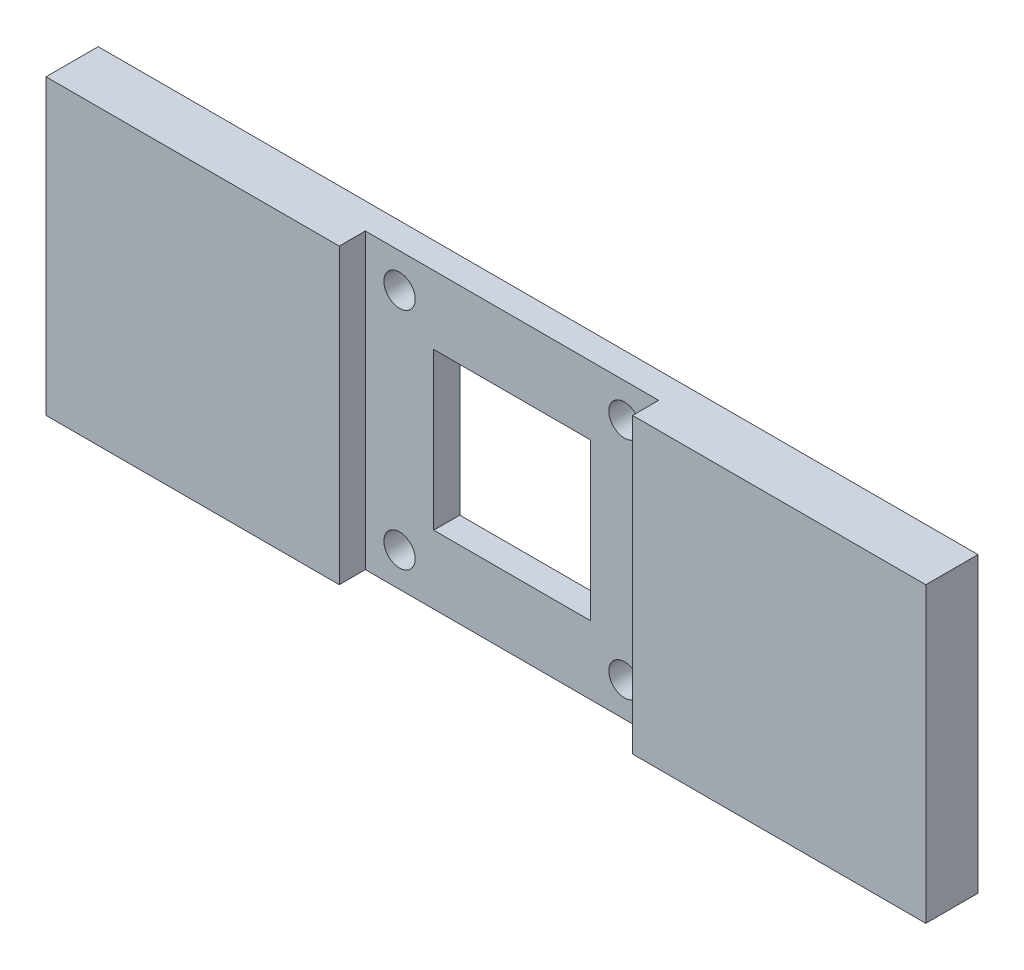
SolidWorks part; units mm, degrees
ref_plane "Front Plane" through (0, 0, 0) normal (0, 0, 1) x (1, 0, 0)
ref_plane "Top Plane" through (0, 0, 0) normal (0, 1, 0) x (1, 0, 0)
ref_plane "Right Plane" through (0, 0, 0) normal (1, 0, 0) x (0, 0, -1)
sketch "Sketch1" plane through (0, 0, 0) normal (0, 0, 1) x (1, 0, 0)
  line L1 (-175, -28.1) -> (175, -28.1)
  line L2 (-175, -28.1) -> (-175, 28.1)
  line L3 (-175, 28.1) -> (175, 28.1)
  line L4 (175, -28.1) -> (175, 28.1)
  line L5 (-175, -28.1) -> (175, 28.1) construction
  line L6 (-175, 28.1) -> (175, -28.1) construction
  point P0 (0, 0)
extrude "Boss-Extrude1" add sketch "Sketch1" along normal blind 10
sketch "Sketch2" plane through (0, 0, 10) normal (0, 0, 1) x (1, 0, 0)
  line L2 (175, 28.1) -> (-175, 28.1) construction
  line L3 (-28.1, -28.1) -> (28.1, -28.1)
  line L4 (-28.1, -28.1) -> (-28.1, 28.1)
  line L5 (-28.1, 28.1) -> (28.1, 28.1)
  line L6 (28.1, -28.1) -> (28.1, 28.1)
  point P8 (0, 0)
extrude "Cut-Extrude1" cut sketch "Sketch2" against normal blind 5
sketch "Sketch3" plane through (175, 0, 0) normal (1, 0, 0) x (0, 0, -1)
  line L1 (-10, 28.1) -> (0, 28.1)
  line L2 (-10, 28.1) -> (-10, -28.1)
  line L3 (-10, -28.1) -> (0, -28.1)
  line L4 (0, 28.1) -> (0, -28.1)
extrude "Boss-Extrude2" add sketch "Sketch3" along normal blind 10
sketch "Sketch4" plane through (0, 0, 10) normal (0, 0, 1) x (1, 0, 0)
  line L0 (28.1, -28.1) -> (185, -28.1) construction
  line L1 (185, 28.1) -> (175, 28.1)
  line L2 (185, 28.1) -> (185, -28.1)
  line L3 (185, -28.1) -> (175, -28.1)
  line L4 (175, 28.1) -> (175, -28.1)
extrude "Boss-Extrude3" add sketch "Sketch4" along normal blind 10
sketch "Sketch5" plane through (0, 28.1, 0) normal (0, 1, 0) x (1, 0, 0)
  line L0 (175, -20) -> (185, -10)
  line L1 (185, 0) -> (185, -20) construction
  line L2 (185, -10) -> (185, -20)
  line L3 (185, -20) -> (175, -20)
extrude "Cut-Extrude2" cut sketch "Sketch5" against normal blind 56.2
sketch "Sketch6" plane through (-175, 0, 0) normal (-1, 0, 0) x (0, 0, 1)
  line L1 (0, -28.1) -> (10, -28.1)
  line L2 (0, -28.1) -> (0, 28.1)
  line L3 (0, 28.1) -> (10, 28.1)
  line L4 (10, -28.1) -> (10, 28.1)
extrude "Boss-Extrude4" add sketch "Sketch6" along normal blind 10
sketch "Sketch7" plane through (0, 0, 10) normal (0, 0, 1) x (1, 0, 0)
  line L0 (-28.1, 28.1) -> (-185, 28.1) construction
  line L1 (-185, -28.1) -> (-175, -28.1)
  line L2 (-185, -28.1) -> (-185, 28.1)
  line L3 (-185, 28.1) -> (-175, 28.1)
  line L4 (-175, -28.1) -> (-175, 28.1)
extrude "Boss-Extrude5" add sketch "Sketch7" along normal blind 10
sketch "Sketch8" plane through (0, 28.1, 0) normal (0, 1, 0) x (1, 0, 0)
  line L0 (-175, -20) -> (-185, -10)
  line L1 (-185, -20) -> (-185, 0) construction
  line L2 (-185, -10) -> (-185, -20)
  line L3 (-185, -20) -> (-175, -20)
extrude "Cut-Extrude3" cut sketch "Sketch8" against normal blind 56.2
sketch "Sketch9" plane through (0, 0, 5) normal (0, 0, 1) x (1, 0, 0)
  line L3 (-15, -15) -> (15, -15)
  line L4 (-15, -15) -> (-15, 15)
  line L5 (-15, 15) -> (15, 15)
  line L6 (15, -15) -> (15, 15)
  point P4 (0, 0)
extrude "Cut-Extrude4" cut sketch "Sketch9" against normal blind 5
sketch "Sketch10" plane through (0, 0, 5) normal (0, 0, 1) x (1, 0, 0)
  circle A2 centre (21.55, 21.55) radius 3
  circle A3 centre (-21.55, -21.55) radius 3
  circle A4 centre (-21.55, 21.55) radius 3
  circle A5 centre (21.55, -21.55) radius 3
extrude "Cut-Extrude5" cut sketch "Sketch10" against normal blind 5
sketch "Sketch11" plane through (97.5, 0, 97.5) normal (0.7071, 0, 0.7071) x (0.7071, 0, -0.7071)
  line L3 (117.9226, -7.5) -> (115.4226, -7.5)
  line L4 (117.9226, -7.5) -> (117.9226, 7.5)
  line L5 (117.9226, 7.5) -> (115.4226, 7.5)
  line L6 (115.4226, -7.5) -> (115.4226, 7.5)
  line L7 (117.9226, -7.5) -> (115.4226, 7.5) construction
  line L8 (117.9226, 7.5) -> (115.4226, -7.5) construction
  point P6 (116.6726, 0)
extrude "Cut-Extrude6" cut sketch "Sketch11" against normal blind 7
sketch "Sketch12" plane through (-97.5, 0, 97.5) normal (-0.7071, 0, 0.7071) x (0.7071, 0, 0.7071)
  line L2 (-117.9226, 7.5) -> (-115.4226, 7.5)
  line L3 (-117.9226, 7.5) -> (-117.9226, -7.5)
  line L4 (-117.9226, -7.5) -> (-115.4226, -7.5)
  line L5 (-115.4226, 7.5) -> (-115.4226, -7.5)
  line L6 (-117.9226, 7.5) -> (-115.4226, -7.5) construction
  line L7 (-117.9226, -7.5) -> (-115.4226, 7.5) construction
  point P4 (-116.6726, 0)
extrude "Cut-Extrude7" cut sketch "Sketch12" against normal blind 7
sketch "Sketch13" plane through (0, 0, 10) normal (0, 0, 1) x (1, 0, 0)
  line L0 (28.1, -28.1) -> (175, -28.1) construction
  line L5 (-175, -28.1) -> (-28.1, -28.1) construction
  line L11 (-84.3, 28.1) -> (-185, 28.1)
  line L12 (-84.3, 28.1) -> (-84.3, -28.1)
  line L13 (-84.3, -28.1) -> (-185, -28.1)
  line L14 (-185, 28.1) -> (-185, -28.1)
  line L15 (84.3, 28.1) -> (185, 28.1)
  line L16 (84.3, 28.1) -> (84.3, -28.1)
  line L17 (84.3, -28.1) -> (185, -28.1)
  line L18 (185, 28.1) -> (185, -28.1)
extrude "Cut-Extrude9" cut sketch "Sketch13" against normal blind 10
